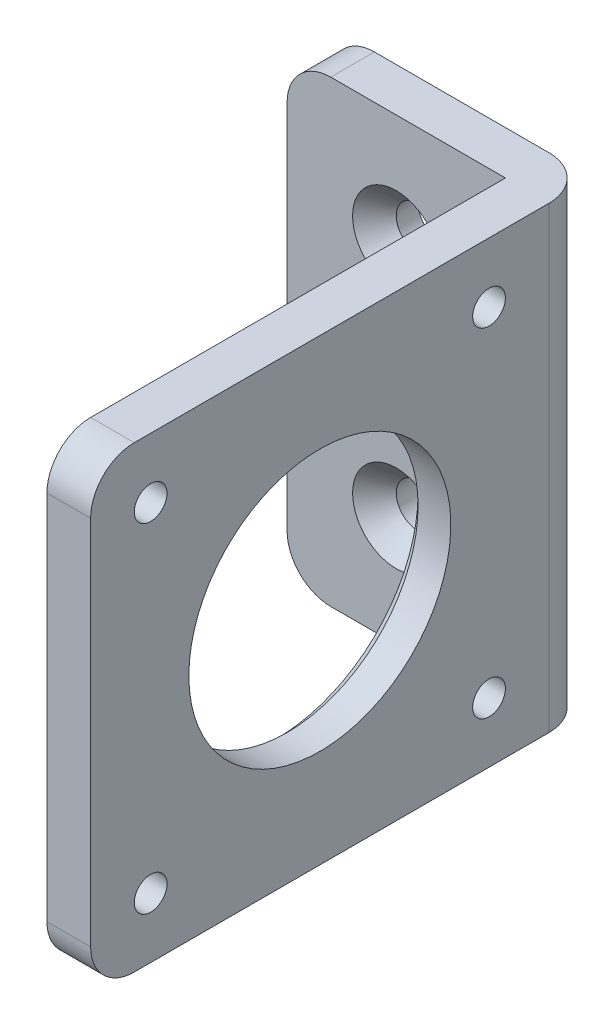
SolidWorks part; units mm, degrees
ref_plane "Front Plane" through (0, 0, 0) normal (0, 0, 1) x (1, 0, 0)
ref_plane "Top Plane" through (0, 0, 0) normal (0, 1, 0) x (1, 0, 0)
ref_plane "Right Plane" through (0, 0, 0) normal (1, 0, 0) x (0, 0, -1)
sketch "Sketch1" plane through (0, 0, 0) normal (0, 1, 0) x (1, 0, 0)
  line L0 (0, 0) -> (0, 42)
  line L1 (0, -55) -> (0, 55) construction
  line L2 (0, 42) -> (-20, 42)
  line L3 (-20, 42) -> (-20, 46)
  line L4 (-20, 46) -> (4, 46)
  line L5 (4, 46) -> (4, 0)
  line L6 (-55, 0) -> (55, 0) construction
  line L7 (4, 0) -> (0, 0)
extrude "Boss-Extrude1" add sketch "Sketch1" along normal blind 42
sketch "Sketch2" plane through (0, 0, 0) normal (-1, 0, 0) x (0, 0, 1)
  line L0 (-42, 21) -> (0, 21) construction
  line L1 (-42, 42) -> (-42, 0) construction
  line L2 (0, 21) -> (-21, 0) construction
  line L3 (-42, 0) -> (0, 0) construction
  line L4 (-21, 0) -> (-21, 5.5) construction
  line L5 (-42, 42) -> (0, 42) construction
  line L7 (-35, 5.5) -> (-36.5, 5.5)
  line L8 (-21, 21) -> (-21, 42) construction
  circle A0 centre (-21, 21) radius 12
  circle A1 centre (-36.5, 5.5) radius 1.5
  circle A2 centre (-5.5, 5.5) radius 1.5
  circle A3 centre (-5.5, 36.5) radius 1.5
  circle A4 centre (-36.5, 36.5) radius 1.5
  dimension "D1" = 15.5
  dimension "D2" = 24
extrude "Cut-Extrude1" cut sketch "Sketch2" against normal through all contours A0 | A4 | A3 | A2 | A1
sketch "Sketch3" plane through (0, 0, -42) normal (0, 0, 1) x (1, 0, 0)
  line L0 (-10, 0) -> (-10, 42) construction
  line L1 (-20, 0) -> (0, 0) construction
  line L2 (-20, 42) -> (0, 42) construction
  line L3 (-10, 42) -> (-10, 32) construction
  line L4 (-10, 21) -> (-20, 21) construction
  line L5 (-20, 42) -> (-20, 0) construction
  circle A0 centre (-10, 32) radius 2
  circle A1 centre (-10, 10) radius 2
extrude "Cut-Extrude2" cut sketch "Sketch3" against normal through all contours A0 | A1
chamfer "Chamfer1" distance 2 angle 45 2 edges at (-8, 32, -42) (-8, 10, -42)
chamfer "Chamfer2" distance 1 angle 45 1 edges at (0, 21, -9)
fillet "Fillet1" radius 4 5 edges at (4, 21, -46) (2, 0, 0) (2, 42, 0) (-20, 0, -44) (-20, 42, -44)
